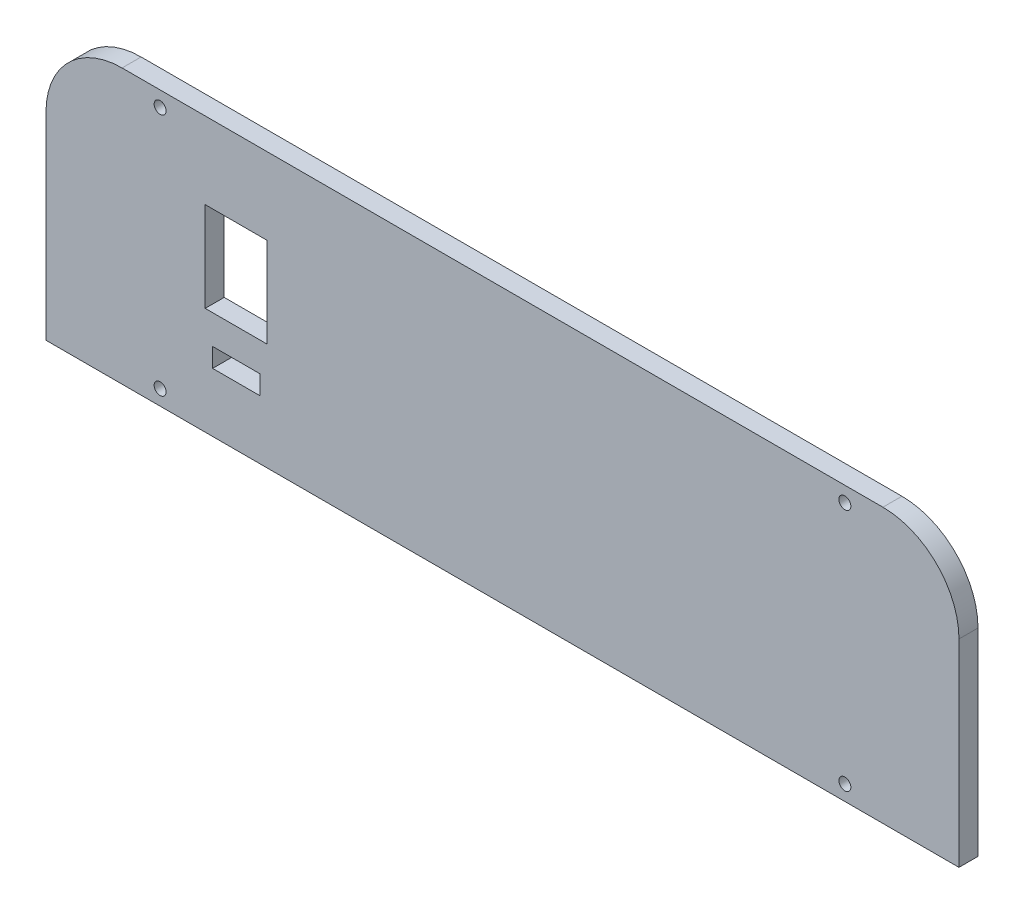
SolidWorks part; units mm, degrees
ref_plane "Front Plane" through (0, 0, 0) normal (0, 0, 1) x (1, 0, 0)
ref_plane "Top Plane" through (0, 0, 0) normal (0, 1, 0) x (1, 0, 0)
ref_plane "Right Plane" through (0, 0, 0) normal (1, 0, 0) x (0, 0, -1)
sketch "Sketch1" plane through (0, 0, 0) normal (0, 0, 1) x (1, 0, 0)
  line L1 (-76.2, -22.86) -> (76.2, -22.86)
  line L2 (-76.2, -22.86) -> (-76.2, 22.86)
  line L3 (-76.2, 22.86) -> (76.2, 22.86)
  line L4 (76.2, -22.86) -> (76.2, 22.86)
  line L5 (-76.2, -22.86) -> (76.2, 22.86) construction
  line L6 (-76.2, 22.86) -> (76.2, -22.86) construction
  point P0 (0, 0)
  dimension "D1" = 152.4
  dimension "D2" = 45.72
extrude "Boss-Extrude1" add sketch "Sketch1" along normal blind 3.175
fillet "Fillet1" radius 12.7 2 edges at (76.2, 22.86, 1.5875) (-76.2, 22.86, 1.5875)
sketch "Sketch2" plane through (0, 0, 3.175) normal (0, 0, 1) x (1, 0, 0)
  line L0 (-76.2, -22.86) -> (76.2, -22.86) construction
  line L1 (-76.2, 10.16) -> (-76.2, -22.86) construction
  line L2 (1.7463, 0) -> (-1.7463, 0) construction
  line L3 (0, -1.7463) -> (0, 1.7463) construction
  circle A0 centre (-57.15, -20.32) radius 1
  circle A1 centre (-57.15, 20.32) radius 1
  circle A2 centre (57.15, -20.32) radius 1
  circle A3 centre (57.15, 20.32) radius 1
  dimension "D1" = 2
  dimension "D2" = 2.54
  dimension "D3" = 19.05
extrude "Cut-Extrude1" cut sketch "Sketch2" against normal through all
sketch "Sketch3" plane through (0, 0, 3.175) normal (0, 0, 1) x (1, 0, 0)
  line L0 (-76.2, -22.86) -> (76.2, -22.86) construction
  line L1 (-48.387, -13.0175) -> (-40.513, -13.0175)
  line L2 (-48.387, -13.0175) -> (-48.387, -9.8425)
  line L3 (-48.387, -9.8425) -> (-40.513, -9.8425)
  line L4 (-40.513, -13.0175) -> (-40.513, -9.8425)
  line L5 (-48.387, -13.0175) -> (-40.513, -9.8425) construction
  line L6 (-48.387, -9.8425) -> (-40.513, -13.0175) construction
  line L7 (-76.2, 10.16) -> (-76.2, -22.86) construction
  point P0 (-44.45, -11.43)
  point P7 (0, 0)
  dimension "D1" = 7.874
  dimension "D2" = 3.175
  dimension "D3" = 11.43
  dimension "D4" = 31.75
extrude "Cut-Extrude2" cut sketch "Sketch3" against normal through all
sketch "Sketch4" plane through (0, 0, 3.175) normal (0, 0, 1) x (1, 0, 0)
  line L0 (-76.2, 10.16) -> (-76.2, -22.86) construction
  line L1 (-49.625, 10.04) -> (-39.275, 10.04)
  line L2 (-49.625, 10.04) -> (-49.625, -4.96)
  line L3 (-49.625, -4.96) -> (-39.275, -4.96)
  line L4 (-39.275, 10.04) -> (-39.275, -4.96)
  line L5 (-49.625, 10.04) -> (-39.275, -4.96) construction
  line L6 (-49.625, -4.96) -> (-39.275, 10.04) construction
  line L7 (-76.2, -22.86) -> (76.2, -22.86) construction
  point P0 (-44.45, 2.54)
  point P5 (-44.6823, 4.9184)
  dimension "D1" = 10.35
  dimension "D2" = 15
  dimension "D3" = 31.75
  dimension "D4" = 25.4
extrude "Cut-Extrude3" cut sketch "Sketch4" against normal through all
